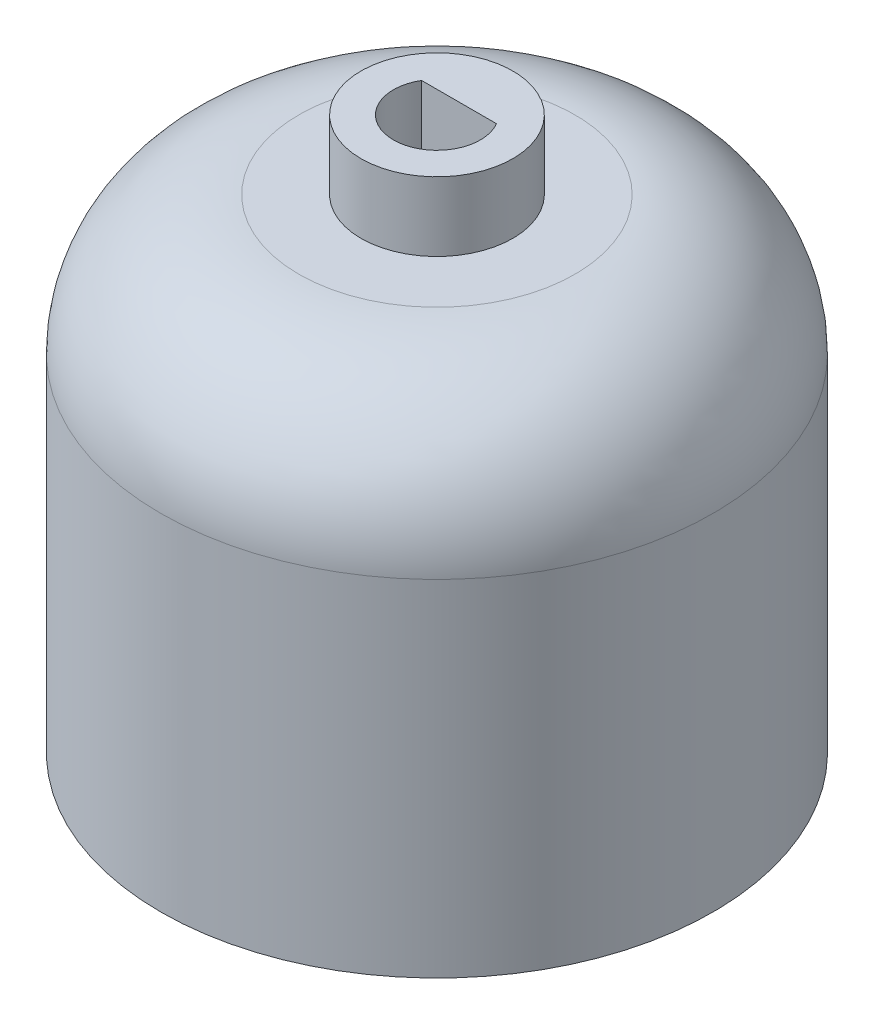
SolidWorks part; units mm, degrees
ref_plane "Front Plane" through (0, 0, 0) normal (0, 0, 1) x (1, 0, 0)
ref_plane "Top Plane" through (0, 0, 0) normal (0, 1, 0) x (1, 0, 0)
ref_plane "Right Plane" through (0, 0, 0) normal (1, 0, 0) x (0, 0, -1)
sketch "Sketch1" plane through (0, 0, 0) normal (0, 1, 0) x (1, 0, 0)
  line L0 (0, 17.6) -> (0, 7.9154) construction
  line L1 (-4.4, 17.6) -> (4.4, 17.6)
  line L2 (-4.4, 17.6) -> (-4.4, 12.0732)
  line L4 (4.4, 17.6) -> (4.4, 12.0732)
  arc A0 (-4.4, 12.0732) -> (4.4, 12.0732) centre (0, 0) ccw
  circle A1 centre (0, 0) radius 20
  dimension "D1" = 25.7
  dimension "D4" = 40
  dimension "D2" = 8.8
  dimension "D3" = 17.6
extrude "Boss-Extrude1" add sketch "Sketch1" along normal blind 30
sketch "Sketch2" plane through (0, 30, 0) normal (0, 1, 0) x (1, 0, 0)
  circle A0 centre (0, 0) radius 20 construction
  circle A1 centre (0, 0) radius 20
extrude "Boss-Extrude2" add sketch "Sketch2" along normal blind 5
sketch "Sketch3" plane through (0, 35, 0) normal (0, 1, 0) x (1, 0, 0)
  line L0 (-2.7134, 1.6) -> (2.7134, 1.6)
  arc A0 (-2.7134, 1.6) -> (2.7134, 1.6) centre (0, 0) ccw
  circle A1 centre (0, 0) radius 20 construction
  circle A2 centre (0, 0) radius 5.5
  dimension "D1" = 6.3
  dimension "D3" = 11
  dimension "D2" = 1.6
extrude "Boss-Extrude3" add sketch "Sketch3" along normal blind 5
fillet "Fillet1" radius 10 1 edges at (0, 35, 20)
